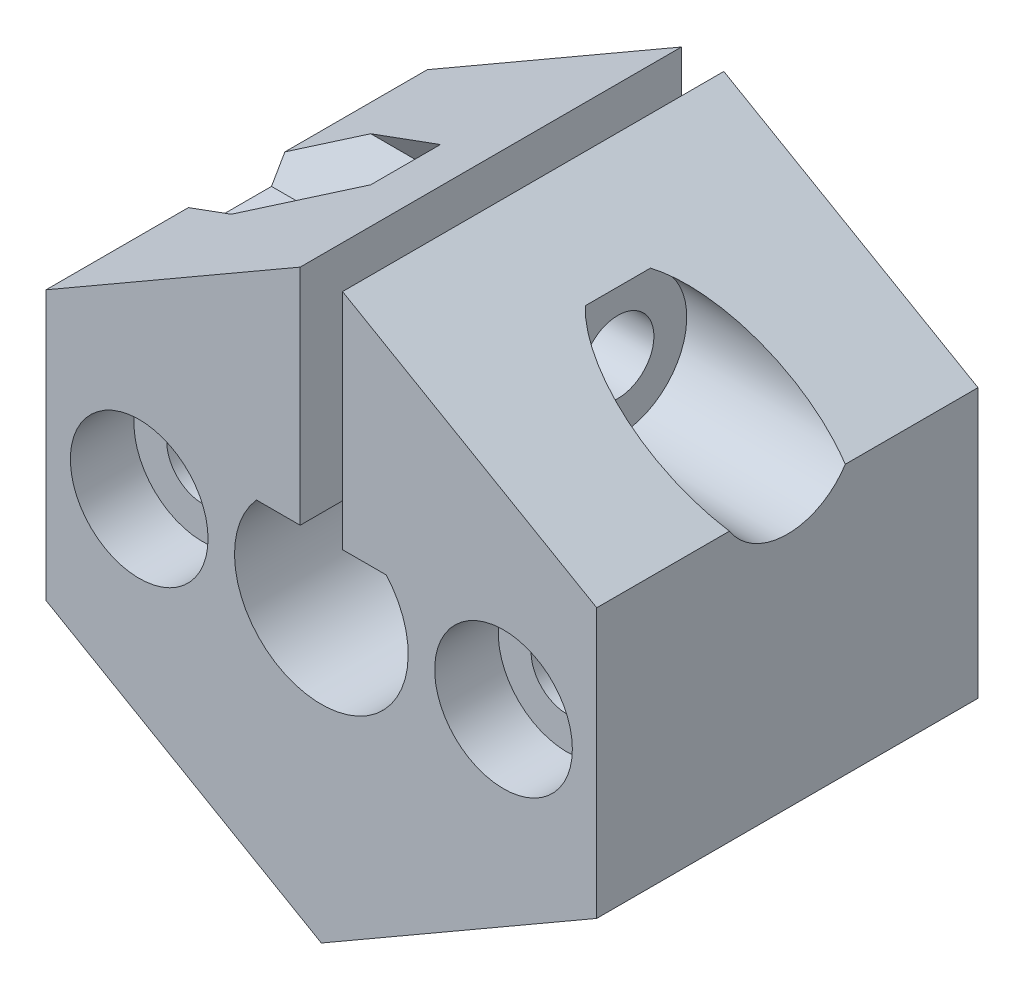
SolidWorks part; units mm, degrees
ref_plane "Front Plane" through (0, 0, 0) normal (1, 0, 0) x (0, 1, 0)
ref_plane "Top Plane" through (0, 0, 0) normal (0, 0, 1) x (0, 1, 0)
ref_plane "Right Plane" through (0, 0, 0) normal (0, 1, 0) x (-1, 0, 0)
sketch "Sketch1" plane through (0, 0, 0) normal (0, 0, 1) x (0, 1, 0)
  line L0 (11.7143, 0) -> (-11.7143, 0) construction
  line L1 (0, 4.1) -> (0, 0) construction
  line L10 (6.3509, -13) -> (-6.3509, -13)
  line L11 (-13.8564, 0) -> (-6.3509, -13)
  line L12 (-6.9282, -12) -> (6.9282, -12) construction
  line L13 (6.3509, -13) -> (13.2791, -1)
  line L14 (13.2791, 1) -> (6.3509, 13)
  line L15 (6.9282, 12) -> (-6.9282, 12) construction
  line L16 (-6.3509, 13) -> (-13.8564, 0)
  line L17 (13.2791, 1) -> (2.725, 1)
  line L18 (13.2791, -1) -> (2.725, -1)
  line L20 (6.3509, 13) -> (-6.3509, 13)
  line L21 (2.9286, 1) -> (2.725, 1) construction
  line L22 (2.725, -3.0634) -> (2.725, -1)
  line L23 (2.725, 1) -> (2.725, 3.0634)
  arc A1 (2.725, 3.0634) -> (-4.1, 0) centre (0, 0) ccw
  arc A2 (-4.1, 0) -> (2.725, -3.0634) centre (0, 0) ccw
  circle A3 centre (0, 0) radius 12 construction
  point P6 (0, 0)
  point P9 (0, 0)
  point P12 (0, 4.1)
  point P13 (0, 4.1)
  point P21 (2.9286, 0)
  point P26 (8.2516, 0)
  point P29 (8.2516, 1)
  point P32 (8.2516, -1)
  point P34 (0, 13)
  point P35 (2.725, 1)
  dimension "D1" = 4.1
  dimension "D2" = 6.1268
extrude "Boss-Extrude1" add sketch "Sketch1" along normal blind 18
ref_plane "Plane1" through (-12, 0, 0) normal (1, 0, 0) x (0, 1, 0)
sketch "Sketch41" plane through (0, 0, 0) normal (0, 0, 1) x (0, 1, 0)
  line L0 (0, 11) -> (0, 4.1) construction
  line L1 (0, -4.1) -> (0, -11) construction
  circle A0 centre (0, 0) radius 11.7143 construction
  arc A1 (2.725, 3.0634) -> (2.725, -3.0634) centre (0, 0) ccw construction
  arc A2 (2.725, 3.0634) -> (2.725, -3.0634) centre (0, 0) ccw construction
  circle A3 centre (0, 0) radius 11.7143 construction
  circle A4 centre (0, 8.6) radius 1.7
  circle A5 centre (0, -8.6) radius 1.7
extrude "Cut-Extrude7" cut sketch "Sketch41" along normal blind 18
ref_plane "nut vertical" through (0, 7.77, 0) normal (0, 1, 0) x (-1, 0, 0)
ref_plane "Plane21" through (0, 0, 9) normal (0, 0, 1) x (0, 1, 0)
hole_wizard "CBORE for M3 SHCS1" positions "3DSketch1" profile "Sketch47" counterbore size "M3" standard "ANSI Metric" end condition through all
sketch3d "3DSketch1"
  line L0 (-8.6, 0, 18) -> (-8.6, 0, 0) construction
  point P0 (-8.6, 0, 18)
sketch "Sketch47" plane through (-8.6, 0, 18) normal (1, 0, 0) x (0, -1, 0)
  line L0 (0, 0) -> (0, 18)
  line L1 (0, 18) -> (1.7, 18)
  line L3 (1.7, 18) -> (1.7, 3)
  line L4 (1.7, 3) -> (3.25, 3)
  line L5 (3.25, 3) -> (3.25, 0)
  line L7 (3.25, 0) -> (0, 0)
  line L11 (0, -6.35) -> (0, 107.95) construction
  dimension "Thru Hole Dia." = 3.4
  dimension "Thru Hole Depth" = 18
  dimension "C'Bore Dia." = 6.5
  dimension "C'Bore Depth" = 3
hole_wizard "CBORE for M3 SHCS2" positions "3DSketch3" profile "Sketch49" counterbore size "M3" standard "ANSI Metric" end condition through all
sketch3d "3DSketch3"
  line L0 (8.6, 0, 18) -> (8.6, 0, 0) construction
  point P0 (8.6, 0, 18)
sketch "Sketch49" plane through (8.6, 0, 18) normal (1, 0, 0) x (0, -1, 0)
  line L0 (0, 0) -> (0, 18)
  line L1 (0, 18) -> (1.7, 18)
  line L3 (1.7, 18) -> (1.7, 3)
  line L4 (1.7, 3) -> (3.25, 3)
  line L5 (3.25, 3) -> (3.25, 0)
  line L7 (3.25, 0) -> (0, 0)
  line L11 (0, -6.35) -> (0, 107.95) construction
  dimension "Thru Hole Dia." = 3.4
  dimension "Thru Hole Depth" = 18
  dimension "C'Bore Dia." = 6.5
  dimension "C'Bore Depth" = 3
ref_plane "Plane22" through (-1, 0, 0) normal (1, 0, 0) x (0, 1, 0)
ref_plane "Plane23" through (-8, 0, 0) normal (1, 0, 0) x (0, 1, 0)
ref_plane "Plane24" through (13, 0, 0) normal (1, 0, 0) x (0, 1, 0)
sketch "Sketch50" plane through (-8, 0, 0) normal (1, 0, 0) x (0, 1, 0)
  line L0 (0, 0) -> (0, 18) construction
  line L19 (0, 9) -> (-13.8564, 9) construction
  line L20 (-13.8564, 18) -> (-13.8564, 0) construction
  line L40 (-1, 0) -> (-1, 18) construction
  line L42 (8.1064, 0) -> (8.1064, 4.25) construction
  line L43 (8.1064, 18) -> (8.1064, 13.75) construction
  line L44 (8.1064, 0) -> (8.1064, 18) construction
  line L45 (5.3364, 5.8493) -> (5.3364, 2.6507)
  line L46 (5.3364, 2.6507) -> (8.1064, 1.0515)
  line L47 (8.1064, 1.0515) -> (10.8764, 2.6507)
  line L48 (10.8764, 2.6507) -> (10.8764, 5.8493)
  line L49 (10.8764, 5.8493) -> (8.1064, 7.4485)
  line L50 (5.3364, 15.3493) -> (8.1064, 16.9485)
  line L51 (5.3364, 12.1507) -> (5.3364, 15.3493)
  line L52 (8.1064, 10.5515) -> (5.3364, 12.1507)
  line L53 (10.8764, 12.1507) -> (8.1064, 10.5515)
  line L54 (10.8764, 15.3493) -> (10.8764, 12.1507)
  line L55 (8.1064, 16.9485) -> (10.8764, 15.3493)
  line L56 (8.1064, 7.4485) -> (5.3364, 5.8493)
  circle A2 centre (8.1064, 4.25) radius 2.85 construction
  circle A3 centre (8.1064, 13.75) radius 2.85 construction
  point P33 (-1, 9)
sketch "Sketch52" plane through (-1, 0, 0) normal (1, 0, 0) x (0, 1, 0)
  line L0 (13.2791, 18) -> (13.2791, 0) construction
  circle A4 centre (8.1064, 9) radius 1.7
  dimension "D1" = 3.4
  dimension "D2" = 9
  dimension "D3" = 5.1726
extrude "Cut-Extrude10" cut sketch "Sketch52" against normal blind 15 and the other way blind 15
sketch "Sketch58" plane through (13, 0, 0) normal (1, 0, 0) x (0, 1, 0)
  circle A0 centre (8.1064, 9) radius 3.25
  dimension "D1" = 6.5
extrude "Cut-Extrude11" cut sketch "Sketch58" against normal blind 8 contours A0
sketch "Sketch60" plane through (-8, 0, 0) normal (1, 0, 0) x (0, 1, 0)
  line L1 (8.1064, 5.7091) -> (10.9564, 7.3546)
  line L2 (10.9564, 7.3546) -> (10.9564, 10.6454)
  line L3 (10.9564, 10.6454) -> (8.1064, 12.2909)
  line L4 (8.1064, 12.2909) -> (5.2564, 10.6454)
  line L5 (5.2564, 10.6454) -> (5.2564, 7.3546)
  line L6 (5.2564, 7.3546) -> (8.1064, 5.7091)
  circle A0 centre (8.1064, 9) radius 2.85 construction
extrude "Cut-Extrude12" cut sketch "Sketch60" against normal blind 6 and the other way blind 4
